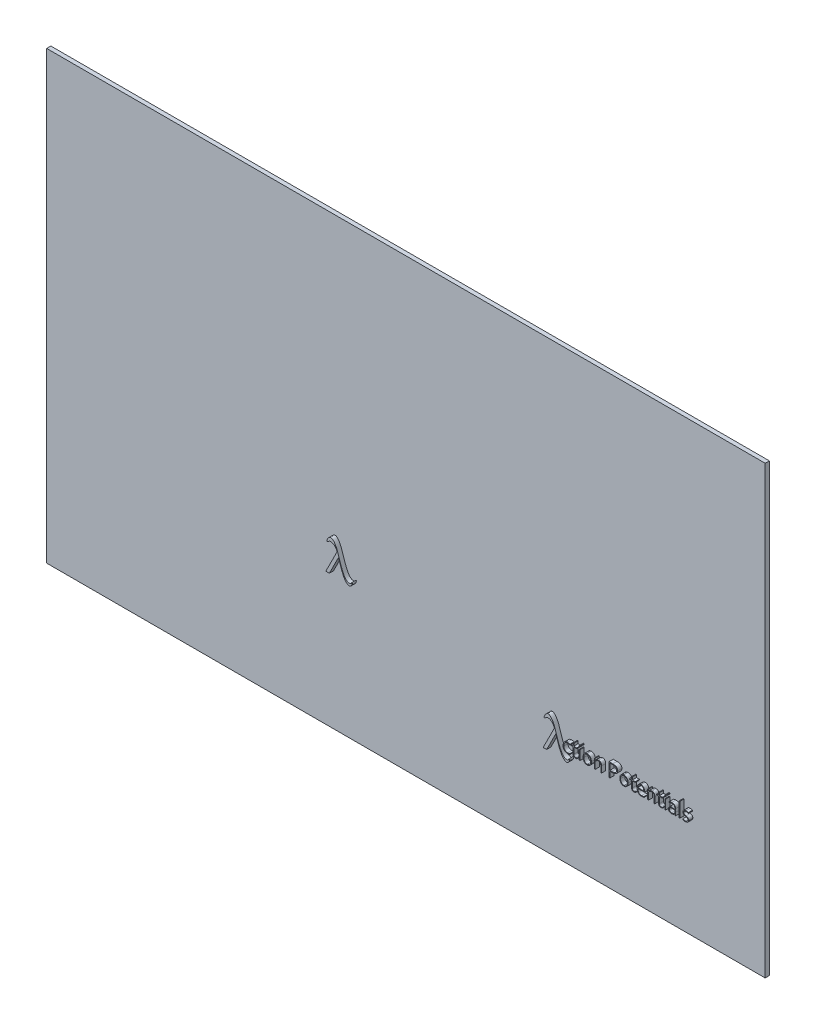
SolidWorks part; units mm, degrees
ref_plane "Front Plane" through (0, 0, 0) normal (0, 0, 1) x (1, 0, 0)
ref_plane "Top Plane" through (0, 0, 0) normal (0, 1, 0) x (1, 0, 0)
ref_plane "Right Plane" through (0, 0, 0) normal (1, 0, 0) x (0, 0, -1)
sketch "Sketch1" plane through (0, 0, 0) normal (0, 0, 1) x (1, 0, 0)
  line L0 (-40.3652, 16.4192) -> (-57.788, -18.2681)
  line L1 (-57.788, -18.2681) -> (-64.6087, -18.2681)
  line L2 (-64.6087, -18.2681) -> (-43.0099, 24.7331)
  spline S0 degree 3 poles (-43.0099, 24.7331) (-44.4112, 28.6306) (-47.02, 33.4464) (-56.4323, 36.6085) (-59.6811, 33.7715) (-62.2584, 31.8311) (-62.8801, 32.9046) (-61.1018, 38.9816) (-53.5737, 46.7371) (-42.807, 30.15) (-38.4283, 13.8731) (-32.8291, -2.7695) (-24.814, -16.3776) (-15.6733, -15.6407) (-15.5447, -12.504) (-13.3968, -12.0906) (-14.6191, -16.2729) (-15.7462, -18.8595) (-20.6968, -21.3334) (-27.6244, -15.9747) (-33.9177, -3.2563) (-37.9545, 8.7668) (-40.3652, 16.4192) knots 0 0 0 0 0.071329 0.097622 0.136797 0.144195 0.150797 0.158668 0.222903 0.312509 0.404672 0.523846 0.611142 0.632247 0.647251 0.649734 0.664463 0.689621 0.709817 0.743505 0.816933 0.950886 0.950886 0.950886 0.950886
  text T0 "ction Potentials" font "Corbel Light" height in points 100
extrude "Boss-Extrude1" add sketch "Sketch1" along normal blind 8
sketch "Sketch2" plane through (0, 0, 0) normal (0, 0, -1) x (-1, 0, 0)
  line L1 (-353.9376, -196.6543) -> (1026.601, -196.6543)
  line L2 (-353.9376, -196.6543) -> (-353.9376, 659.8915)
  line L3 (-353.9376, 659.8915) -> (1026.601, 659.8915)
  line L4 (1026.601, -196.6543) -> (1026.601, 659.8915)
  line L5 (-353.9376, -196.6543) -> (1026.601, 659.8915) construction
  line L6 (-353.9376, 659.8915) -> (1026.601, -196.6543) construction
  point P0 (336.3317, 231.6186)
extrude "Boss-Extrude2" add sketch "Sketch2" along normal blind 8 separate body
sketch "Sketch3" plane through (0, 0, 8) normal (0, 0, 1) x (1, 0, 0)
  line L0 (-460.6005, 109.2551) -> (-482.1993, 66.254)
  line L1 (-482.1993, 66.254) -> (-475.3786, 66.254)
  line L2 (-475.3786, 66.254) -> (-457.9557, 100.9413)
  spline S0 degree 3 poles (-457.9557, 100.9413) (-455.545, 93.2888) (-451.5083, 81.2657) (-445.215, 68.5473) (-438.2873, 63.1887) (-433.3368, 65.6625) (-432.2097, 68.2492) (-430.9873, 72.4315) (-433.1353, 72.0181) (-433.2638, 68.8813) (-442.4045, 68.1444) (-450.4197, 81.7525) (-456.0189, 98.3952) (-460.3976, 114.6721) (-471.1643, 131.2592) (-478.6923, 123.5037) (-480.4707, 117.4267) (-479.849, 116.3532) (-477.2716, 118.2936) (-474.0229, 121.1306) (-464.6105, 117.9684) (-462.0018, 113.1527) (-460.6005, 109.2551) knots 0 0 0 0 0.133953 0.20738 0.241069 0.261265 0.286423 0.301151 0.303635 0.318639 0.339744 0.42704 0.546214 0.638377 0.727983 0.792218 0.800089 0.806691 0.814089 0.853264 0.879557 0.950886 0.950886 0.950886 0.950886
extrude "Boss-Extrude3" add sketch "Sketch3" against normal up to surface (8 mm away) separate body contours S0 L0 L1 L2 up to face at (-336.3317, 231.6186, 0)
